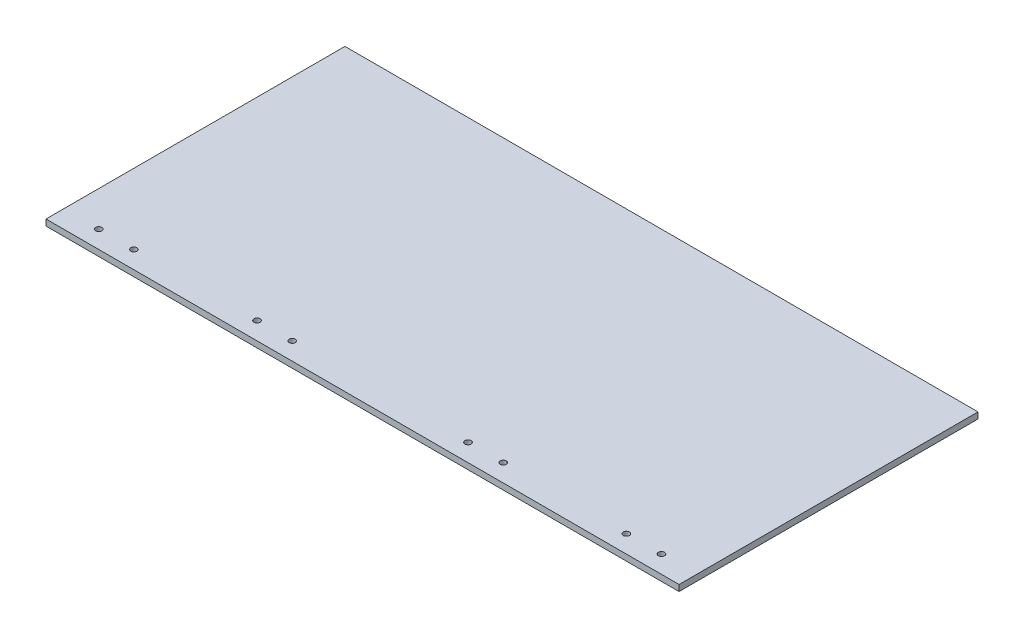
SolidWorks part; units mm, degrees
ref_plane "Front Plane" through (0, 0, 0) normal (0, 0, 1) x (1, 0, 0)
ref_plane "Top Plane" through (0, 0, 0) normal (0, 1, 0) x (1, 0, 0)
ref_plane "Right Plane" through (0, 0, 0) normal (1, 0, 0) x (0, 0, -1)
sketch "Sketch1" plane through (0, 0, 0) normal (0, 1, 0) x (1, 0, 0)
  line L1 (0, 0) -> (360, 0)
  line L2 (0, 0) -> (0, 170)
  line L3 (0, 170) -> (360, 170)
  line L4 (360, 0) -> (360, 170)
  dimension "D1" = 170
  dimension "D2" = 360
extrude "Boss-Extrude1" add sketch "Sketch1" along normal blind 3.5
sketch "Sketch2" plane through (0, 3.5, 0) normal (0, 1, 0) x (1, 0, 0)
  line L0 (0, 10) -> (360, 10) construction
  line L1 (0, 170) -> (0, 0) construction
  line L2 (360, 0) -> (360, 170) construction
  line L3 (0, 0) -> (360, 0) construction
  line L4 (180, 170) -> (180, 0) construction
  line L5 (360, 170) -> (0, 170) construction
  circle A0 centre (20, 10) radius 1.75
  circle A1 centre (40, 10) radius 1.75
  circle A2 centre (110, 10) radius 1.75
  circle A3 centre (130, 10) radius 1.75
  circle A4 centre (230, 10) radius 1.75
  circle A5 centre (250, 10) radius 1.75
  circle A6 centre (320, 10) radius 1.75
  circle A7 centre (340, 10) radius 1.75
  dimension "D2" = 3.5
  dimension "D3" = 20
  dimension "D5" = 20
  dimension "D7" = 70
  dimension "D1" = 10
  dimension "D4" = 2
  dimension "D6" = 2
extrude "Cut-Extrude1" cut sketch "Sketch2" against normal blind 3.5
